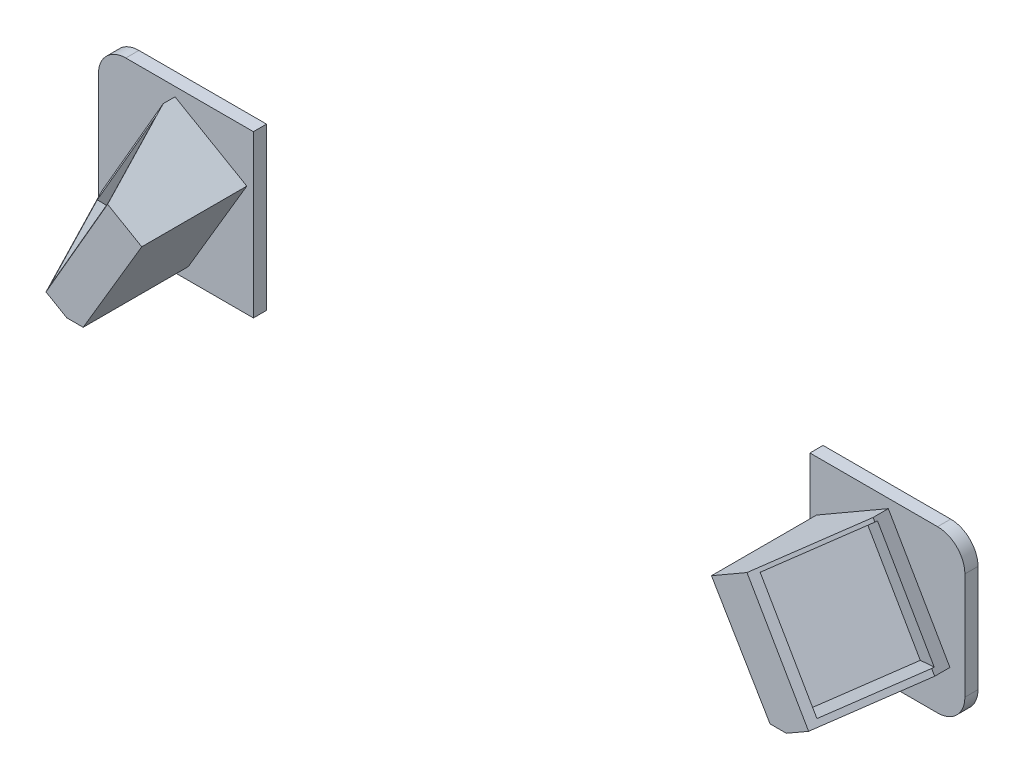
SolidWorks part; units mm, degrees
ref_plane "Ebene vorne" through (0, 0, 0) normal (0, 0, 1) x (1, 0, 0)
ref_plane "Ebene oben" through (0, 0, 0) normal (0, 1, 0) x (1, 0, 0)
ref_plane "Ebene rechts" through (0, 0, 0) normal (1, 0, 0) x (0, 0, -1)
sketch "Skizze1" plane through (0, 0, 200.6848) normal (0, 0, 1) x (1, 0, 0)
  line L0 (42.0463, 20.9394) -> (71.2025, 20.9394)
  line L1 (77.4445, 27.1814) -> (77.4445, 51.5622)
  line L2 (71.2025, 57.8042) -> (42.0463, 57.8042)
  line L3 (42.0463, 57.8042) -> (42.0463, 20.9394)
  line L4 (-85.0991, 57.8042) -> (-85.0991, 20.9394)
  line L5 (-85.0991, 20.9394) -> (-114.2553, 20.9394)
  line L6 (-120.4973, 27.1814) -> (-120.4973, 51.5622)
  line L7 (-114.2553, 57.8042) -> (-85.0991, 57.8042)
  arc A0 (71.2025, 20.9394) -> (77.4445, 27.1814) centre (71.2025, 27.1814) ccw
  arc A1 (77.4445, 51.5622) -> (71.2025, 57.8042) centre (71.2025, 51.5622) ccw
  arc A2 (-114.2553, 20.9394) -> (-120.4973, 27.1814) centre (-114.2553, 27.1814) cw
  arc A3 (-120.4973, 51.5622) -> (-114.2553, 57.8042) centre (-114.2553, 51.5622) cw
extrude "Aufsatz-Linear austragen1" add sketch "Skizze1" along normal blind 3
sketch "Skizze3" plane through (0, 0, 203.6848) normal (0, 0, 1) x (1, 0, 0)
  line L0 (59.9536, 55.7457) -> (74.0305, 31.3638)
  line L1 (74.0305, 31.3638) -> (60.6666, 23.6481)
  line L2 (60.6666, 23.6481) -> (56.936, 23.6481)
  line L3 (56.936, 23.6481) -> (43.5515, 46.276)
  line L4 (43.5515, 46.276) -> (59.9536, 55.7457)
  line L5 (66.063, 43.2991) -> (59.763, 54.211) construction
  line L6 (65.3566, 28.2674) -> (59.0775, 24.6422) construction
  line L9 (59.763, 54.211) -> (52.809, 50.1961) construction
  line L10 (-21.5264, -59.1171) -> (-21.5264, 108.3718) construction
  line L12 (20.9357, -31.8652) -> (20.9357, 19.4394) construction
  line L13 (-63.9885, 19.4394) -> (-63.9885, -31.8652) construction
  line L14 (-103.0064, 55.7457) -> (-117.0833, 31.3638)
  line L15 (-117.0833, 31.3638) -> (-103.7194, 23.6481)
  line L16 (-103.7194, 23.6481) -> (-99.9888, 23.6481)
  line L17 (-99.9888, 23.6481) -> (-86.6043, 46.276)
  line L18 (-86.6043, 46.276) -> (-103.0064, 55.7457)
extrude "Aufsatz-Linear austragen2" add sketch "Skizze3" along normal blind 24
sketch "Skizze4" plane through (4.9267, -8.5333, 0) normal (0.5, -0.866, 0) x (-0.866, -0.5, 0)
  line L0 (-80.4973, -205.6624) -> (-69.0169, -230.2821)
  line L1 (-69.0169, -230.2821) -> (-80.4973, -230.2821)
  line L2 (-80.4973, -230.2821) -> (-80.4973, -205.6624)
  line L3 (-70.8248, -225.3317) -> (-78.8545, -208.1118) construction
extrude "Schnitt-Linear austragen2" cut sketch "Skizze4" against normal through all
sketch "Skizze6" plane through (-15.6899, -27.1757, 0) normal (-0.5, -0.866, 0) x (0.866, -0.5, 0)
  line L0 (-117.901, 204.6244) -> (-104.6836, 232.9693)
  line L1 (-104.6836, 232.9693) -> (-117.901, 232.9693)
  line L2 (-117.901, 232.9693) -> (-117.901, 204.6244)
  line L3 (-115.5405, 208.8144) -> (-107.5108, 226.0343) construction
extrude "Schnitt-Linear austragen3" cut sketch "Skizze6" against normal blind 54
sketch "Skizze7" plane through (-151.744, 87.6094, 81.7059) normal (-0.7849, 0.4532, 0.4226) x (0.366, -0.2113, 0.9063)
  line L1 (160.3583, -3.595) -> (140.2063, -3.595)
  line L2 (160.3583, -3.595) -> (160.3583, -30.4912)
  line L3 (160.3583, -30.4912) -> (140.2063, -30.4912)
  line L4 (140.2063, -3.595) -> (140.2063, -30.4912)
extrude "Schnitt-Linear austragen4" cut sketch "Skizze7" against normal blind 9
sketch "Skizze8" plane through (125.4812, 72.4466, 67.5648) normal (0.7849, 0.4532, 0.4226) x (0.366, 0.2113, -0.9063)
  line L1 (-174.6363, -8.4745) -> (-153.5122, -8.4745)
  line L2 (-174.6363, -8.4745) -> (-174.6363, 17.4671)
  line L3 (-174.6363, 17.4671) -> (-153.5122, 17.4671)
  line L4 (-153.5122, -8.4745) -> (-153.5122, 17.4671)
extrude "Schnitt-Linear austragen5" cut sketch "Skizze8" against normal blind 9
